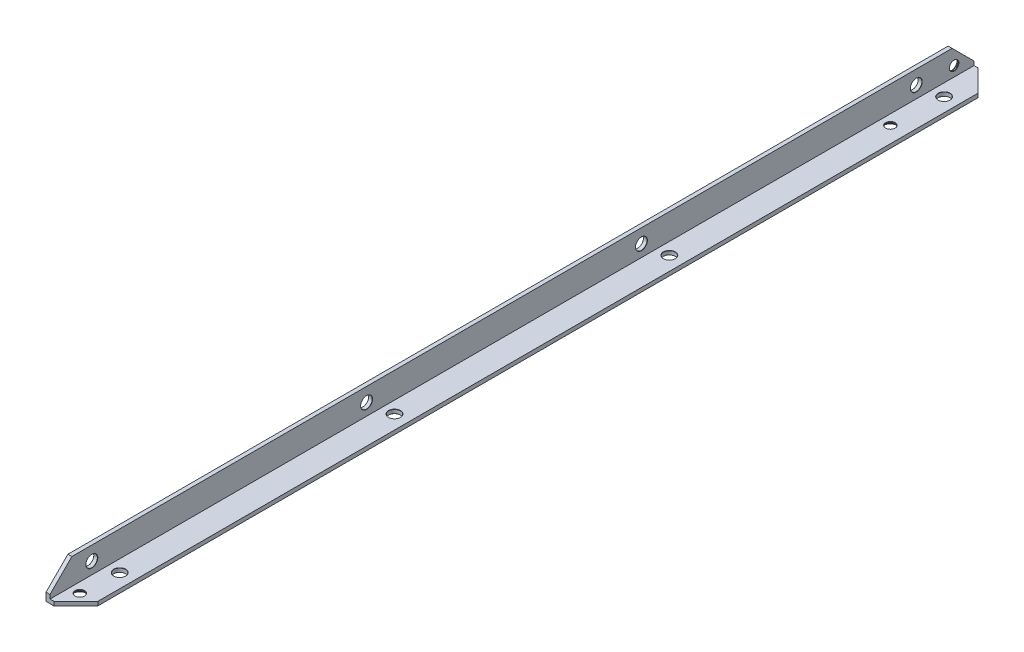
SolidWorks part; units mm, degrees
ref_plane "Спереди" through (0, 0, 0) normal (0, 0, 1) x (1, 0, 0)
ref_plane "Сверху" through (0, 0, 0) normal (0, 1, 0) x (1, 0, 0)
ref_plane "Справа" through (0, 0, 0) normal (1, 0, 0) x (0, 0, -1)
sketch "Эскиз1" plane through (0, 0, 0) normal (0, 0, 1) x (1, 0, 0)
  line L0 (0, 0) -> (0, 15)
  line L1 (0, 15) -> (2, 15)
  line L2 (2, 15) -> (2, 2)
  line L3 (2, 2) -> (15, 2)
  line L4 (15, 2) -> (15, 0)
  line L5 (15, 0) -> (0, 0)
  dimension "D1" = 2
  dimension "D2" = 15
extrude "Бобышка-Вытянуть1" add sketch "Эскиз1" along normal blind 464
chamfer "Фаска1" distance 11 angle 45 4 edges at (1, 15, 0) (15, 1, 0) (15, 1, 464) (1, 15, 464)
hole_wizard "Зенковка для винта с потайной головкой M41" positions "Эскиз3" profile "Эскиз2" countersink size "M4" standard "DIN" end condition through all
sketch "Эскиз3" plane through (0, 0, 0) normal (0, -1, 0) x (1, 0, 0)
  line L0 (0, 464) -> (0, 0) construction
  line L3 (0, 464) -> (4, 464) construction
  line L4 (0, 0) -> (4, 0) construction
  point P0 (7, 454)
  point P13 (7, 47)
  dimension "D1" = 7
  dimension "D2" = 10
  dimension "D3" = 47
sketch "Эскиз2" plane through (7, 0, 454) normal (1, 0, 0) x (0, 0, -1)
  line L0 (0, 0) -> (0, 2)
  line L1 (0, 2) -> (2.4, 2)
  line L2 (2.25, 1.85) -> (2.25, 1.45)
  line L3 (2.25, 1.45) -> (3.7, 0)
  line L5 (3.7, 0) -> (0, 0)
  line L6 (-2.25, 1.45) -> (-3.7, 0) construction
  line L7 (2.4, 2) -> (2.25, 1.85)
  line L8 (-2.4, 2) -> (-2.25, 1.85) construction
  line L11 (0, -6.35) -> (0, 107.95) construction
  dimension "Диаметр сквозного отверстия" = 4.5
  dimension "Глубина сквозного отверстия" = 2
  dimension "Диаметр передней зенковки" = 7.4
  dimension "Угол передней зенковки" = 90
  dimension "Диаметр задней зенковки" = 4.8
  dimension "Угол задней зенковки" = 90
hole_wizard "Зенковка для винта с потайной головкой M42" positions "Эскиз7" profile "Эскиз6" countersink size "M4" standard "DIN" end condition through all
sketch "Эскиз7" plane through (0, 0, 0) normal (-1, 0, 0) x (0, 0, 1)
  line L0 (464, 0) -> (0, 0) construction
  line L1 (0, 4) -> (0, 0) construction
  point P4 (10, 7)
  dimension "D1" = 7
  dimension "D2" = 10
sketch "Эскиз6" plane through (0, 7, 10) normal (0, 1, 0) x (0, 0, 1)
  line L0 (0, 0) -> (0, 2)
  line L1 (0, 2) -> (2.4, 2)
  line L2 (2.25, 1.85) -> (2.25, 1.45)
  line L3 (2.25, 1.45) -> (3.7, 0)
  line L5 (3.7, 0) -> (0, 0)
  line L6 (-2.25, 1.45) -> (-3.7, 0) construction
  line L7 (2.4, 2) -> (2.25, 1.85)
  line L8 (-2.4, 2) -> (-2.25, 1.85) construction
  line L11 (0, -6.35) -> (0, 107.95) construction
  dimension "Диаметр сквозного отверстия" = 4.5
  dimension "Глубина сквозного отверстия" = 2
  dimension "Диаметр передней зенковки" = 7.4
  dimension "Угол передней зенковки" = 90
  dimension "Диаметр задней зенковки" = 4.8
  dimension "Угол задней зенковки" = 90
hole_wizard "Отверстие с зазором M51" positions "Эскиз9" profile "Эскиз8" hole size "M5" standard "Ansi (метрические)" end condition up to next
sketch "Эскиз9" plane through (0, 0, 0) normal (-1, 0, 0) x (0, 0, 1)
  line L0 (464, 0) -> (0, 0) construction
  circle A0 centre (10, 7) radius 3.7 construction
  point P1 (29, 8)
  point P4 (167, 8)
  point P7 (305, 8)
  point P10 (443, 8)
  dimension "D2" = 19
  dimension "D1" = 8
  dimension "D3" = 138
  dimension "D4" = 138
  dimension "D5" = 138
sketch "Эскиз8" plane through (0, 8, 29) normal (0, 1, 0) x (0, 0, 1)
  line L0 (0, 0) -> (0, 2)
  line L1 (0, 2) -> (3, 2)
  line L2 (2.9, 1.9) -> (2.9, 0.1)
  line L3 (2.9, 0.1) -> (3, 0)
  line L5 (3, 0) -> (0, 0)
  line L6 (-2.9, 0.1) -> (-3, 0) construction
  line L7 (3, 2) -> (2.9, 1.9)
  line L8 (-3, 2) -> (-2.9, 1.9) construction
  line L11 (0, -6.35) -> (0, 107.95) construction
  dimension "Диаметр сквозного отверстия" = 5.8
  dimension "Глубина сквозного отверстия" = 2
  dimension "Диаметр передней зенковки" = 6
  dimension "Угол передней зенковки" = 90
  dimension "Диаметр задней зенковки" = 6
  dimension "Угол задней зенковки" = 90
hole_wizard "Отверстие с зазором M52" positions "Эскиз11" profile "Эскиз10" hole size "M5" standard "Ansi (метрические)" end condition up to next
sketch "Эскиз11" plane through (0, 0, 0) normal (0, -1, 0) x (1, 0, 0)
  line L0 (0, 0) -> (4, 0) construction
  line L1 (0, 464) -> (0, 0) construction
  point P1 (8, 21)
  point P4 (8, 159)
  point P7 (8, 297)
  point P10 (8, 435)
  dimension "D1" = 21
  dimension "D2" = 138
  dimension "D3" = 138
  dimension "D4" = 138
  dimension "D5" = 8
sketch "Эскиз10" plane through (8, 0, 21) normal (1, 0, 0) x (0, 0, -1)
  line L0 (0, 0) -> (0, 2)
  line L1 (0, 2) -> (3, 2)
  line L2 (2.9, 1.9) -> (2.9, 0.1)
  line L3 (2.9, 0.1) -> (3, 0)
  line L5 (3, 0) -> (0, 0)
  line L6 (-2.9, 0.1) -> (-3, 0) construction
  line L7 (3, 2) -> (2.9, 1.9)
  line L8 (-3, 2) -> (-2.9, 1.9) construction
  line L11 (0, -6.35) -> (0, 107.95) construction
  dimension "Диаметр сквозного отверстия" = 5.8
  dimension "Глубина сквозного отверстия" = 2
  dimension "Диаметр передней зенковки" = 6
  dimension "Угол передней зенковки" = 90
  dimension "Диаметр задней зенковки" = 6
  dimension "Угол задней зенковки" = 90
